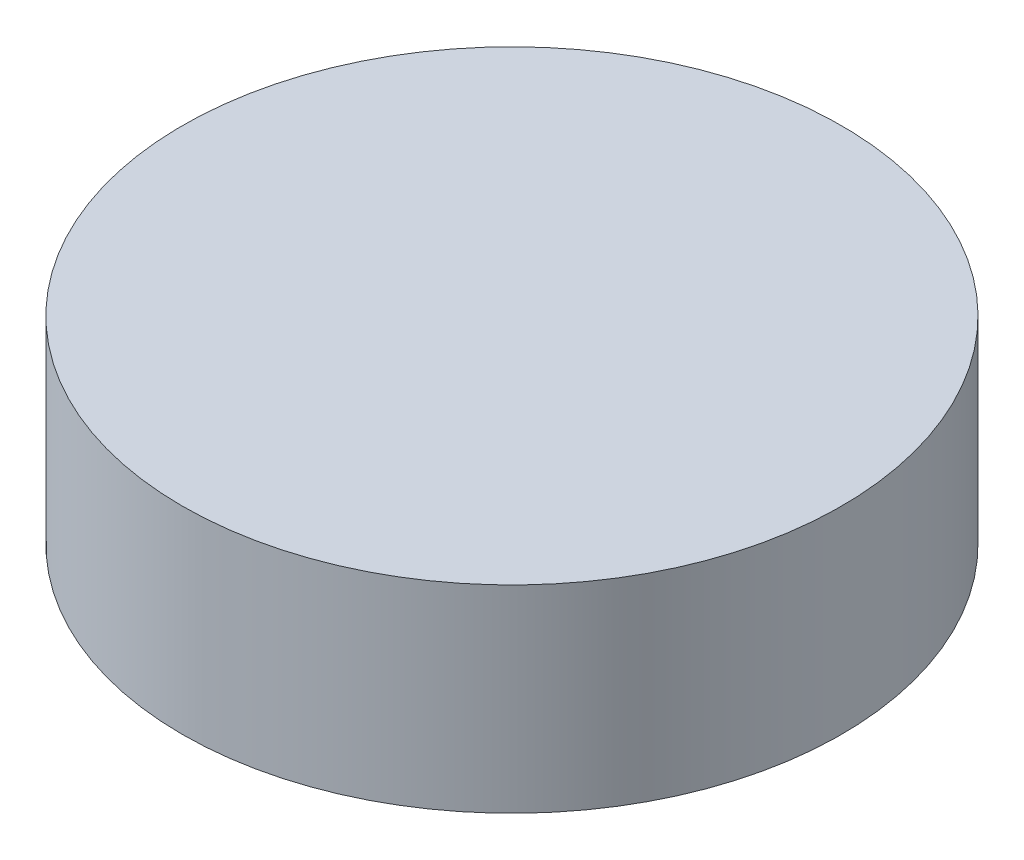
SolidWorks part; units mm, degrees
ref_plane "Front" through (0, 0, 0) normal (0, 0, 1) x (1, 0, 0)
ref_plane "Top" through (0, 0, 0) normal (0, 1, 0) x (1, 0, 0)
ref_plane "Right" through (0, 0, 0) normal (1, 0, 0) x (0, 0, -1)
sketch "Sketch2" plane through (0, 0, 0) normal (0, 1, 0) x (1, 0, 0)
  circle A0 centre (0, 0) radius 10
  dimension "D1" = 20
extrude "Boss-Extrude1" add sketch "Sketch2" along normal mid plane 6
sketch "Sketch4" plane through (0, -3, 0) normal (0, -1, 0) x (-1, 0, 0)
  circle A0 centre (0, 0) radius 3
  dimension "D1" = 6
extrude "Cut-Extrude2" cut sketch "Sketch4" against normal blind 3
